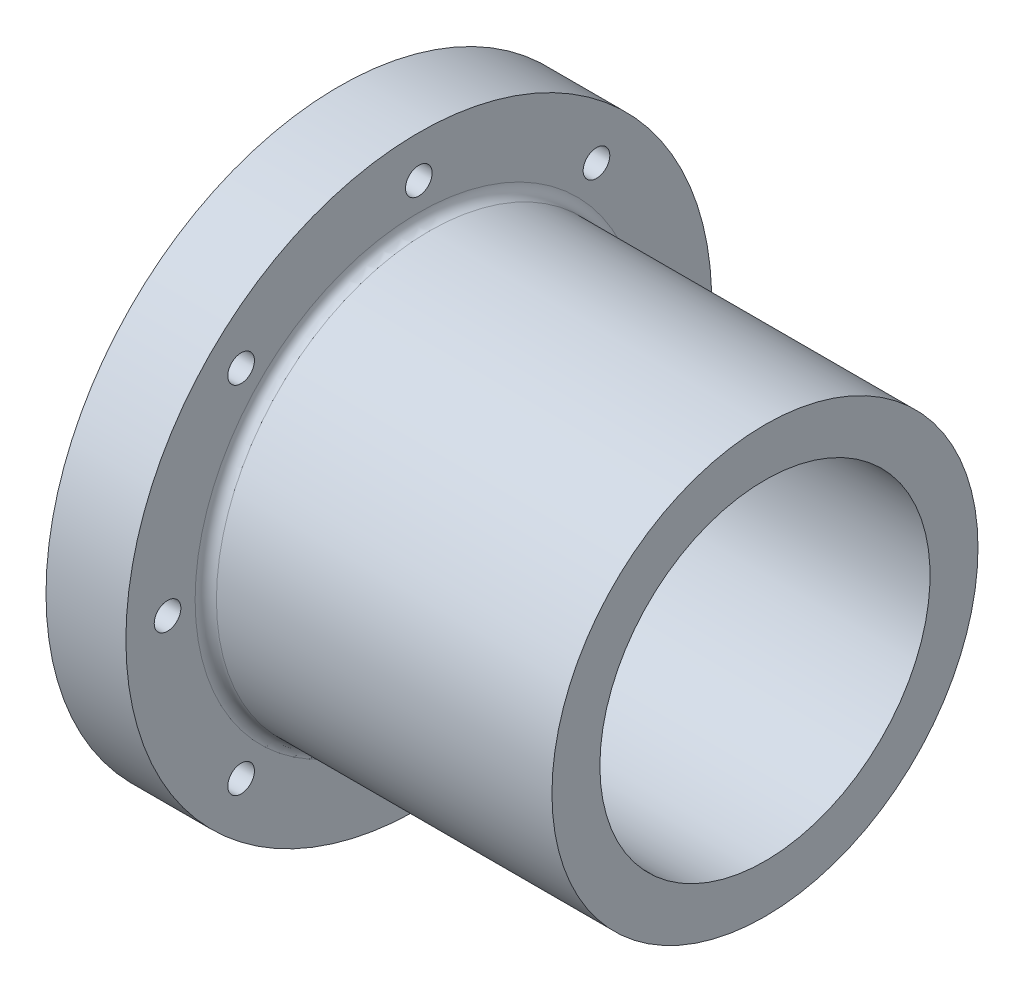
SolidWorks part; units mm, degrees
material "AISI 316 Annealed Stainless Steel Bar (SS)"
ref_plane "Front Plane" through (0, 0, 0) normal (0, 0, 1) x (1, 0, 0)
ref_plane "Top Plane" through (0, 0, 0) normal (0, 1, 0) x (1, 0, 0)
ref_plane "Right Plane" through (0, 0, 0) normal (1, 0, 0) x (0, 0, -1)
sketch "Sketch1" plane through (0, 0, 0) normal (0, 0, 1) x (1, 0, 0)
  line L0 (0, 0) -> (215.3765, 0) construction
  line L1 (0, 0) -> (0, 93.6004) construction
  line L23 (-30.1096, 50.8) -> (-30.1096, 39.37)
  line L24 (-30.1096, 50.8) -> (-30.1096, 69.85)
  line L25 (-30.1096, 69.85) -> (-11.0596, 69.85)
  line L26 (-11.0596, 69.85) -> (-11.0596, 50.8)
  line L30 (71.4904, 50.8) -> (-11.0596, 50.8)
  line L32 (-30.1096, 39.37) -> (-13.5996, 39.37)
  line L33 (-13.5996, 39.37) -> (-13.5996, 11.43)
  line L34 (-13.5996, 11.43) -> (-0.8996, 11.43)
  line L35 (-0.8996, 11.43) -> (-0.8996, 39.37)
  line L36 (-0.8996, 39.37) -> (71.4904, 39.37)
  line L37 (71.4904, 39.37) -> (71.4904, 50.8)
  point P6 (0, 0)
  dimension "D1" = 101.6
  dimension "D2" = 11.43
  dimension "D3" = 12.7
  dimension "D4" = 19.05
  dimension "D5" = 16.51
  dimension "D6" = 19.05
  dimension "D7" = 11.43
  dimension "D8" = 69.85
revolve "Revolve1" add sketch "Sketch1" angle 360 about L0
sketch "Sketch3" plane through (-30.1096, 0, 0) normal (-1, 0, 0) x (0, 0, 1)
  circle A0 centre (0, 59.9186) radius 3.175
  circle A1 centre (42.3688, 42.3688) radius 3.175
  circle A2 centre (59.9186, 0) radius 3.175
  circle A3 centre (42.3688, -42.3688) radius 3.175
  circle A4 centre (0, -59.9186) radius 3.175
  circle A5 centre (-42.3688, -42.3688) radius 3.175
  circle A6 centre (-59.9186, 0) radius 3.175
  circle A7 centre (-42.3688, 42.3688) radius 3.175
  point P36 (0, 0)
  dimension "D1" = 6.35
  dimension "D2" = 59.9186
  dimension "D3" = 8
extrude "Cut-Extrude2" cut sketch "Sketch3" against normal up to next
fillet "Fillet2" radius 2.54 3 edges at (-11.0596, 0, 50.8) (-13.5996, 0, 39.37) (-0.8996, 0, 39.37)
hole_wizard "CBORE for #8 Socket Head Cap Screw1" positions "Sketch7" profile "Sketch5" counterbore size "#8" standard "ANSI Inch" end condition through all
sketch "Sketch7" plane through (-13.5996, 0, 0) normal (-1, 0, 0) x (0, 0, 1)
  point P0 (0, -25.4)
  point P4 (-25.4, 0)
  point P6 (25.4, 0)
  point P8 (0, 25.4)
  point P15 (0, 0)
  point P16 (0, 0)
  point P17 (0, 0)
  point P18 (0, 0)
  point P19 (0, 0)
  dimension "D1" = 25.4
  dimension "D2" = 25.4
  dimension "D3" = 25.4
  dimension "D4" = 25.4
sketch "Sketch5" plane through (-13.5996, -25.4, 0) normal (0, 1, 0) x (0, 0, 1)
  line L0 (0, 0) -> (0, 85.09)
  line L1 (0, 85.09) -> (2.2479, 85.09)
  line L3 (2.2479, 85.09) -> (2.2479, 4.1656)
  line L4 (3.9688, 4.1656) -> (2.2479, 4.1656)
  line L5 (3.9688, 4.1656) -> (3.9688, 1.4287)
  line L6 (3.9688, 1.4287) -> (5.3975, 0)
  line L7 (5.3975, 0) -> (0, 0)
  line L8 (-3.9688, 1.4287) -> (-5.3975, 0) construction
  line L11 (0, -6.35) -> (0, 107.95) construction
  dimension "Thru Hole Dia." = 4.4958
  dimension "Thru Hole Depth" = 85.09
  dimension "C'Bore Dia." = 7.9375
  dimension "C'Bore Depth" = 4.1656
  dimension "Near C'Sink Dia." = 10.795
  dimension "Near C'Sink Angle" = 90
fillet "Fillet3" radius 2.54 2 edges at (-0.8996, 0, 11.43) (-13.5996, 0, 11.43)
sketch "Sketch8" plane through (-30.1096, 0, 0) normal (-1, 0, 0) x (0, 0, 1)
  circle A0 centre (0, 0) radius 50.8
  dimension "D1" = 101.6
extrude "Cut-Extrude3" cut sketch "Sketch8" against normal blind 3.175
fillet "Fillet4" radius 1.27 1 edges at (-26.9346, 0, 50.8)
hole_wizard "3/16 (0.1875) Diameter Hole1" positions "Sketch9" profile "Sketch10" hole size "3/16" standard "ANSI Inch"
sketch "Sketch9" plane through (-26.9346, 0, 0) normal (-1, 0, 0) x (0, 0, 1)
  point P0 (-44.45, 0)
  point P5 (0, 44.45)
  point P7 (44.45, 0)
  point P9 (0, -44.45)
  point P16 (44.4967, 0)
  point P19 (0, 0)
  point P20 (0, 0)
  point P21 (0, 0)
  dimension "D1" = 44.45
  dimension "D2" = 44.45
  dimension "D3" = 44.45
  dimension "D4" = 44.45
sketch "Sketch10" plane through (-26.9346, 0, -44.45) normal (0, 1, 0) x (0, 0, 1)
  line L0 (0, 0) -> (0, 15.4008)
  line L1 (0, 15.4008) -> (2.3812, 13.97)
  line L2 (2.3812, 13.97) -> (2.3812, 0)
  line L5 (2.3812, 0) -> (0, 0)
  line L10 (0, 15.4008) -> (-2.3813, 13.97) construction
  line L11 (0, -6.35) -> (0, 107.95) construction
  dimension "Hole Dia." = 4.7625
  dimension "Hole Depth" = 13.97
  dimension "Drill Angle" = 118
chamfer "Chamfer2" distance 1.27 angle 45 1 edges at (-26.9346, 0, 39.37)
